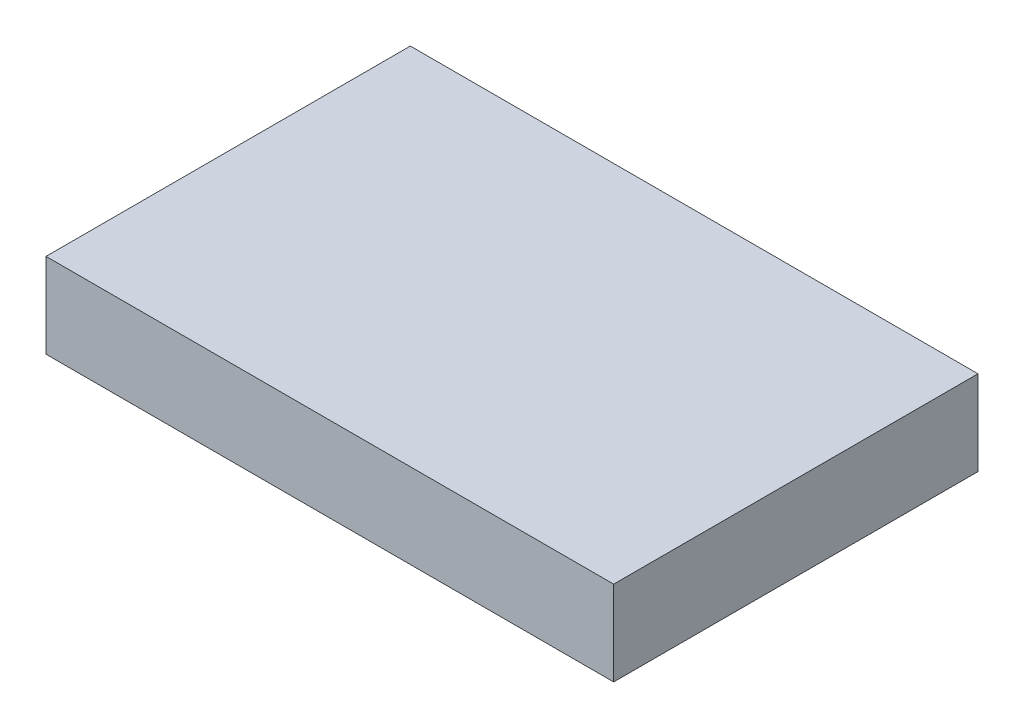
SolidWorks part; units mm, degrees
ref_plane "Front Plane" through (0, 0, 0) normal (0, 0, 1) x (1, 0, 0)
ref_plane "Top Plane" through (0, 0, 0) normal (0, 1, 0) x (1, 0, 0)
ref_plane "Right Plane" through (0, 0, 0) normal (1, 0, 0) x (0, 0, -1)
sketch "Sketch1" plane through (0, 0, 0) normal (0, 1, 0) x (1, 0, 0)
  line L1 (0, 0) -> (17.018, 0)
  line L2 (0, 0) -> (0, 10.922)
  line L3 (0, 10.922) -> (17.018, 10.922)
  line L4 (17.018, 0) -> (17.018, 10.922)
  dimension "D1" = 17.018
  dimension "D2" = 10.922
extrude "Boss-Extrude1" add sketch "Sketch1" along normal blind 2.54
